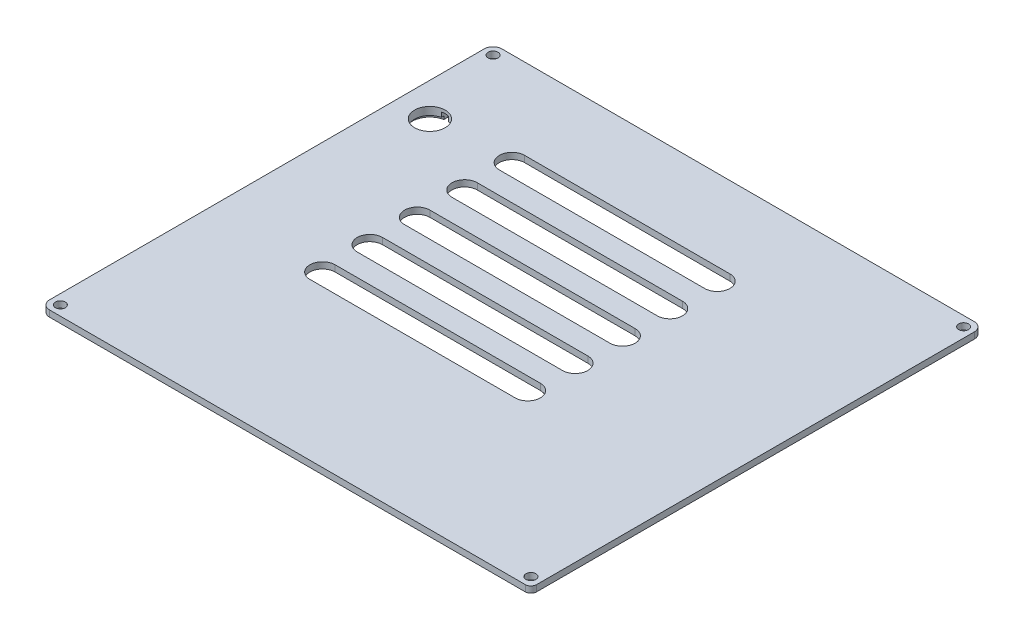
SolidWorks part; units mm, degrees
ref_plane "Front Plane" through (0, 0, 0) normal (0, 0, 1) x (1, 0, 0)
ref_plane "Top Plane" through (0, 0, 0) normal (0, 1, 0) x (1, 0, 0)
ref_plane "Right Plane" through (0, 0, 0) normal (1, 0, 0) x (0, 0, -1)
sketch "Sketch1" plane through (0, 0, 0) normal (0, 1, 0) x (1, 0, 0)
  line L1 (0, 0) -> (156, 0)
  line L2 (0, 0) -> (0, -144)
  line L3 (0, -144) -> (156, -144)
  line L4 (156, 0) -> (156, -144)
  dimension "D1" = 156
  dimension "D2" = 144
extrude "Boss-Extrude1" add sketch "Sketch1" along normal blind 2
sketch "Sketch2" plane through (0, 2, 0) normal (0, 1, 0) x (1, 0, 0)
  line L0 (0, 0) -> (0, -144) construction
  line L1 (3.5, -3.5) -> (152.5, -3.5) construction
  line L2 (3.5, -3.5) -> (3.5, -140.5) construction
  line L3 (3.5, -140.5) -> (152.5, -140.5) construction
  line L4 (152.5, -3.5) -> (152.5, -140.5) construction
  line L5 (152.5, -3.5) -> (152.5, 0) construction
  line L6 (156, 0) -> (0, 0) construction
  line L7 (152.5, -3.5) -> (156, -3.5) construction
  line L8 (156, -144) -> (156, 0) construction
  line L9 (3.5, -140.5) -> (3.5, -144) construction
  line L10 (0, -144) -> (156, -144) construction
  line L11 (3.5, -140.5) -> (0, -140.5) construction
  line L12 (156, -140.5) -> (152.5, -140.5) construction
  line L13 (152.5, -140.5) -> (152.5, -144) construction
  circle A0 centre (3.5, -3.5) radius 1.575
  circle A1 centre (152.5, -3.5) radius 1.575
  circle A2 centre (152.5, -140.5) radius 1.575
  circle A3 centre (3.5, -140.5) radius 1.575
  dimension "D2" = 3.15
  dimension "D1" = 3.5
extrude "Cut-Extrude1" cut sketch "Sketch2" against normal blind 5
sketch "Sketch3" plane through (0, 2, 0) normal (0, 1, 0) x (1, 0, 0)
  line L0 (36, -30) -> (101, -30) construction
  line L1 (36, -26) -> (101, -26)
  line L2 (36, -34) -> (101, -34)
  line L3 (156, -144) -> (156, 0) construction
  line L4 (156, 0) -> (0, 0) construction
  line L5 (36, -45) -> (101, -45) construction
  line L6 (36, -41) -> (101, -41)
  line L7 (36, -49) -> (101, -49)
  line L8 (36, -60) -> (101, -60) construction
  line L9 (36, -56) -> (101, -56)
  line L10 (36, -64) -> (101, -64)
  line L11 (36, -75) -> (101, -75) construction
  line L12 (36, -71) -> (101, -71)
  line L13 (36, -79) -> (101, -79)
  line L14 (36, -90) -> (101, -90) construction
  line L15 (36, -86) -> (101, -86)
  line L16 (36, -94) -> (101, -94)
  line L20 (0, 0) -> (0, -144) construction
  arc A0 (36, -26) -> (36, -34) centre (36, -30) ccw
  arc A1 (101, -34) -> (101, -26) centre (101, -30) ccw
  arc A2 (36, -41) -> (36, -49) centre (36, -45) ccw
  arc A3 (101, -49) -> (101, -41) centre (101, -45) ccw
  arc A4 (36, -56) -> (36, -64) centre (36, -60) ccw
  arc A5 (101, -64) -> (101, -56) centre (101, -60) ccw
  arc A6 (36, -71) -> (36, -79) centre (36, -75) ccw
  arc A7 (101, -79) -> (101, -71) centre (101, -75) ccw
  arc A8 (36, -86) -> (36, -94) centre (36, -90) ccw
  arc A9 (101, -94) -> (101, -86) centre (101, -90) ccw
  circle A14 centre (11, -31) radius 4.85
  point P2 (68.5, -30)
  point P14 (68.5, -45)
  point P21 (68.5, -60)
  point P28 (68.5, -75)
  point P35 (68.5, -90)
  dimension "D4" = 4
  dimension "D8" = 11
  dimension "D9" = 9.7
  dimension "D1" = 55
  dimension "D2" = 65
  dimension "D3" = 30
  dimension "D6" = 15
  dimension "D7" = 31
  dimension "D5" = 5
extrude "Cut-Extrude2" cut sketch "Sketch3" against normal blind 50
sketch "Sketch4" plane through (0, 2, 0) normal (0, 1, 0) x (1, 0, 0)
  line L0 (0.2, -143.8) -> (0, -143.8) construction
  line L1 (0.2, -0.2) -> (155.8, -0.2)
  line L2 (0.2, -0.2) -> (0.2, -143.8)
  line L3 (0.2, -143.8) -> (155.8, -143.8)
  line L4 (0, 0) -> (0, -144)
  line L12 (155.8, -0.2) -> (155.8, -143.8)
  line L13 (0.2, -143.8) -> (0.2, -144) construction
  line L14 (0.2, 0) -> (0.2, -0.2) construction
  line L15 (0.2, -0.2) -> (0, -0.2) construction
  line L16 (155.8, 0) -> (155.8, -0.2) construction
  line L17 (155.8, -0.2) -> (156, -0.2) construction
  line L34 (0, 0) -> (0, -144)
  line L38 (0, -144) -> (156, -144)
  line L40 (0, -144) -> (156, -144)
  line L42 (156, -144) -> (156, 0)
  line L43 (156, -144) -> (156, 0)
  line L44 (156, 0) -> (0, 0)
  line L45 (156, 0) -> (0, 0)
  dimension "D2" = 0.2
  dimension "D1" = 0
extrude "Cut-Extrude3" cut sketch "Sketch4" against normal blind 50
fillet "Fillet1" radius 3 3 edges at (0.2, 1, 143.8) (155.8, 1, 0.2) (0.2, 1, 0.2)
fillet "Fillet2" radius 2 1 edges at (155.8, 1, 143.8)
sketch "Sketch5" plane through (0, 0, 0) normal (0, -1, 0) x (1, 0, 0)
  circle A0 centre (11, 31) radius 9
  circle A1 centre (11, 31) radius 4.85
  circle A2 centre (11, 31) radius 4.85 construction
  dimension "D1" = 18
extrude "Boss-Extrude2" add sketch "Sketch5" along normal blind 0.5
sketch "Sketch6" plane through (0, -0.5, 0) normal (0, -1, 0) x (1, 0, 0)
  circle A0 centre (11, 31) radius 5.65
  circle A1 centre (11, 31) radius 9
  circle A2 centre (11, 31) radius 9
  dimension "D2" = 11.3
  dimension "D1" = 0
extrude "Boss-Extrude3" add sketch "Sketch6" along normal blind 1
sketch "Sketch7" plane through (0, -1.5, 0) normal (0, -1, 0) x (1, 0, 0)
  line L0 (11, 31) -> (11, 25.35) construction
  line L1 (9.9, 26.5) -> (12.1, 26.5)
  line L2 (9.9, 26.5) -> (9.9, 24.2)
  line L3 (9.9, 24.2) -> (12.1, 24.2)
  line L4 (12.1, 26.5) -> (12.1, 24.2)
  line L5 (9.9, 26.5) -> (12.1, 24.2) construction
  line L6 (9.9, 24.2) -> (12.1, 26.5) construction
  circle A0 centre (11, 31) radius 5.65 construction
  circle A1 centre (11, 31) radius 5.65 construction
  circle A2 centre (11, 31) radius 4.85 construction
  point P0 (11, 25.35)
  dimension "D1" = 2.2
  dimension "D2" = 6.8
extrude "Cut-Extrude4" cut sketch "Sketch7" against normal blind 2.5
sketch "Sketch8" plane through (0, 2, 0) normal (0, 1, 0) x (1, 0, 0)
  line L8 (3.2, -143.6) -> (153.8, -143.6)
  line L9 (155.6, -141.8) -> (155.6, -3.2)
  line L10 (152.8, -0.4) -> (3.2, -0.4)
  line L11 (0.4, -3.2) -> (0.4, -140.8)
  line L12 (3.2, -143.6) -> (153.8, -143.6)
  line L13 (155.6, -141.8) -> (155.6, -3.2)
  line L14 (152.8, -0.4) -> (3.2, -0.4)
  line L15 (0.4, -3.2) -> (0.4, -140.8)
  line L16 (3.2, -143.8) -> (153.8, -143.8)
  line L17 (155.8, -141.8) -> (155.8, -3.2)
  line L18 (152.8, -0.2) -> (3.2, -0.2)
  line L19 (0.2, -3.2) -> (0.2, -140.8)
  line L20 (3.2, -143.8) -> (153.8, -143.8)
  line L21 (155.8, -141.8) -> (155.8, -3.2)
  line L22 (152.8, -0.2) -> (3.2, -0.2)
  line L23 (0.2, -3.2) -> (0.2, -140.8)
  arc A8 (153.8, -143.6) -> (155.6, -141.8) centre (153.8, -141.8) ccw
  arc A9 (155.6, -3.2) -> (152.8, -0.4) centre (152.8, -3.2) ccw
  arc A10 (3.2, -0.4) -> (0.4, -3.2) centre (3.2, -3.2) ccw
  arc A11 (0.4, -140.8) -> (3.2, -143.6) centre (3.2, -140.8) ccw
  arc A12 (153.8, -143.6) -> (155.6, -141.8) centre (153.8, -141.8) ccw
  arc A13 (155.6, -3.2) -> (152.8, -0.4) centre (152.8, -3.2) ccw
  arc A14 (3.2, -0.4) -> (0.4, -3.2) centre (3.2, -3.2) ccw
  arc A15 (0.4, -140.8) -> (3.2, -143.6) centre (3.2, -140.8) ccw
  arc A16 (153.8, -143.8) -> (155.8, -141.8) centre (153.8, -141.8) ccw
  arc A17 (155.8, -3.2) -> (152.8, -0.2) centre (152.8, -3.2) ccw
  arc A18 (3.2, -0.2) -> (0.2, -3.2) centre (3.2, -3.2) ccw
  arc A19 (0.2, -140.8) -> (3.2, -143.8) centre (3.2, -140.8) ccw
  arc A20 (153.8, -143.8) -> (155.8, -141.8) centre (153.8, -141.8) ccw
  arc A21 (155.8, -3.2) -> (152.8, -0.2) centre (152.8, -3.2) ccw
  arc A22 (3.2, -0.2) -> (0.2, -3.2) centre (3.2, -3.2) ccw
  arc A23 (0.2, -140.8) -> (3.2, -143.8) centre (3.2, -140.8) ccw
  dimension "D1" = 0.2
  dimension "D2" = 0
extrude "Cut-Extrude5" cut sketch "Sketch8" against normal blind 10
